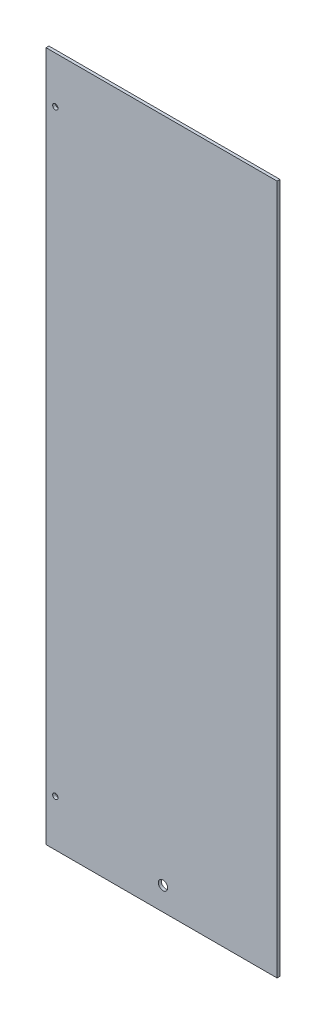
SolidWorks part; units mm, degrees
material "6061 Alloy"
ref_plane "Front" through (0, 0, 0) normal (0, 0, 1) x (1, 0, 0)
ref_plane "Top" through (0, 0, 0) normal (0, 1, 0) x (1, 0, 0)
ref_plane "Right" through (0, 0, 0) normal (1, 0, 0) x (0, 0, -1)
sketch "Sketch1" plane through (0, 0, 0) normal (0, 0, 1) x (1, 0, 0)
  line L1 (0, 0) -> (126.0475, 0)
  line L2 (0, 0) -> (0, 376.555)
  line L3 (0, 376.555) -> (126.0475, 376.555)
  line L4 (126.0475, 0) -> (126.0475, 376.555)
  dimension "D1" = 376.555
  dimension "D2" = 126.0475
extrude "Main Plate" add sketch "Sketch1" along normal blind 1.5875
sketch "Sketch2" plane through (0, 0, 1.5875) normal (0, 0, 1) x (1, 0, 0)
  line L0 (0, 376.555) -> (0, 0) construction
  line L1 (126.0475, 376.555) -> (0, 376.555) construction
  circle A0 centre (5.08, 351.155) radius 1.4605
  dimension "D3" = 2.921
  dimension "D1" = 5.08
  dimension "D2" = 25.4
extrude "Bolt Holes" cut sketch "Sketch2" against normal blind 6.35
pattern_linear "LPattern1" count 2 spacing 325.755 along (0, -1, 0) of "Bolt Holes"
sketch "Sketch3" plane through (0, 0, 1.5875) normal (0, 0, 1) x (1, 0, 0)
  line L0 (0, 376.555) -> (0, 0) construction
  line L1 (0, 0) -> (126.0475, 0) construction
  circle A0 centre (63.8175, 12.7) radius 2.54
  dimension "D1" = 5.08
  dimension "D2" = 63.8175
  dimension "D3" = 12.7
extrude "Wire Hole" cut sketch "Sketch3" against normal blind 6.35
